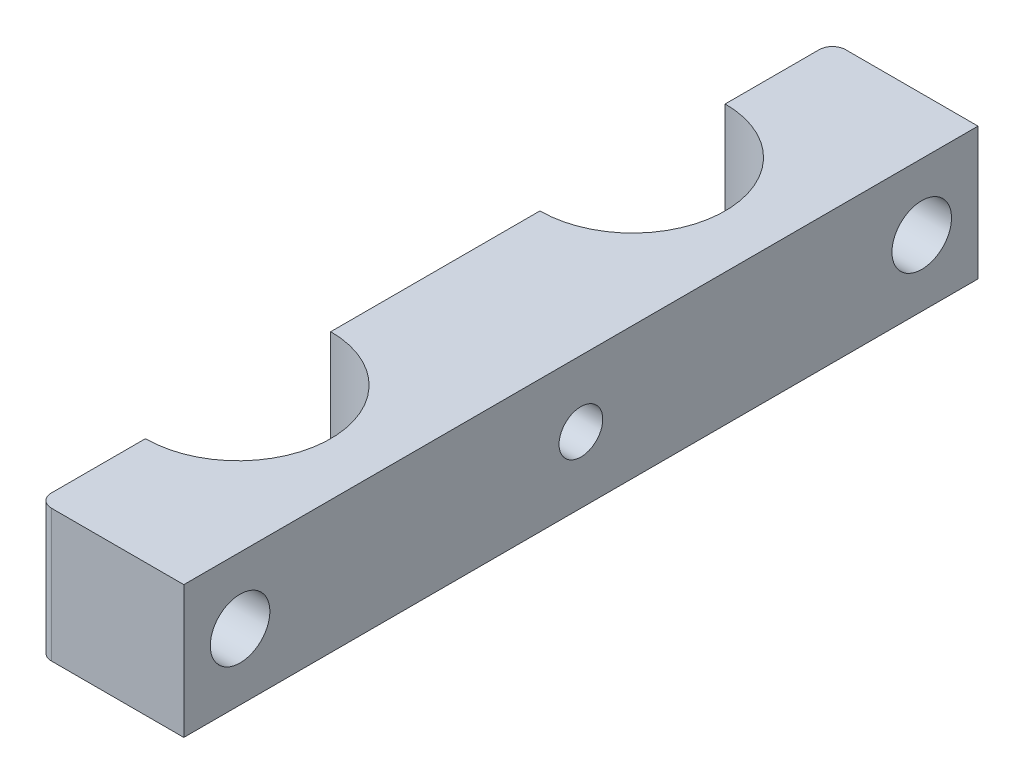
SolidWorks part; units mm, degrees
material "3.1355 (EN-AW 2024)"
ref_plane "Спереди" through (0, 0, 0) normal (0, 0, 1) x (1, 0, 0)
ref_plane "Сверху" through (0, 0, 0) normal (0, 1, 0) x (1, 0, 0)
ref_plane "Справа" through (0, 0, 0) normal (1, 0, 0) x (0, 0, -1)
sketch "Эскиз2" plane through (0, 382.6451, 0) normal (0, 1, 0) x (1, 0, 0)
  line L0 (3.5658, 102.6739) -> (3.5658, 88.6739) construction
  line L1 (14.5658, 80.7739) -> (3.5658, 80.7739) construction
  line L3 (3.5658, 102.6739) -> (3.5658, 110.7739)
  line L4 (3.5658, 88.6739) -> (3.5658, 72.8739)
  line L5 (3.5658, 58.8739) -> (3.5658, 50.7739)
  line L7 (3.5658, 110.7739) -> (14.5658, 110.7739)
  line L8 (14.5658, 110.7739) -> (14.5658, 50.7739)
  line L9 (3.5658, 50.7739) -> (14.5658, 50.7739)
  line L11 (3.5658, 72.8739) -> (3.5658, 58.8739) construction
  line L12 (3.5658, 72.8739) -> (3.5658, 58.8739) construction
  arc A2 (3.5658, 102.6739) -> (3.5658, 88.6739) centre (3.5658, 95.6739) cw
  arc A3 (3.5658, 72.8739) -> (3.5658, 58.8739) centre (3.5658, 65.8739) cw
  dimension "D3" = 7
  dimension "D4" = 7
  dimension "D1" = 60
  dimension "D6" = 29.8
  dimension "D8" = 11
extrude "Бобышка-Вытянуть1" add sketch "Эскиз2" against normal blind 10
fillet "Скругление1" radius 1 2 edges at (3.5658, 377.6451, -50.7739) (3.5658, 377.6451, -110.7739)
hole_wizard "Отверстие с зазором M41" positions "Эскиз3" profile "Эскиз4" hole size "M4" standard "Ansi Metric"
sketch "Эскиз3" plane through (3.5658, 346.9469, -25.6528) normal (-1, 0, 0) x (0, 0, 1)
  point P0 (-80.8711, 30.6982)
  point P3 (-29.3711, 30.6982)
sketch "Эскиз4" plane through (3.5658, 377.6451, -106.5239) normal (0, 1, 0) x (0, 0, 1)
  line L0 (0, 0) -> (0, 12.3509)
  line L1 (0, 12.3509) -> (2.25, 10.999)
  line L2 (2.25, 10.999) -> (2.25, 0)
  line L3 (2.25, 0) -> (0, 0)
  line L4 (0, 12.3509) -> (-2.25, 10.999) construction
  line L5 (0, -6.35) -> (0, 107.95) construction
  dimension "Диаметр отверстия" = 4.5
  dimension "Глубина отверстия" = 10.999
  dimension "Угол заточки сверла" = 118
hole_wizard "Отверстие обработанное метчиком M4x0.71" positions "Эскиз5" profile "Эскиз6" tap size "M4x0.7" standard "Ansi Metric"
sketch "Эскиз5" plane through (3.5658, 346.9469, -25.6528) normal (-1, 0, 0) x (0, 0, 1)
  point P0 (-55.1211, 30.6982)
sketch "Эскиз6" plane through (3.5658, 377.6451, -80.7739) normal (0, 1, 0) x (0, 0, 1)
  line L0 (0, 0) -> (0, 11.9904)
  line L1 (0, 11.9904) -> (1.65, 10.999)
  line L2 (1.65, 10.999) -> (1.65, 0)
  line L3 (1.65, 0) -> (0, 0)
  line L4 (0, 11.9904) -> (-1.65, 10.999) construction
  line L5 (0, -6.35) -> (0, 107.95) construction
  dimension "Диаметр сверла" = 3.3
  dimension "Глубина сверла" = 10.999
  dimension "Угол заточки сверла" = 118
cosmetic thread "Отверстие резьбы1"
equation "\"D3@Эскиз2\"=\"D4@Эскиз2\""
